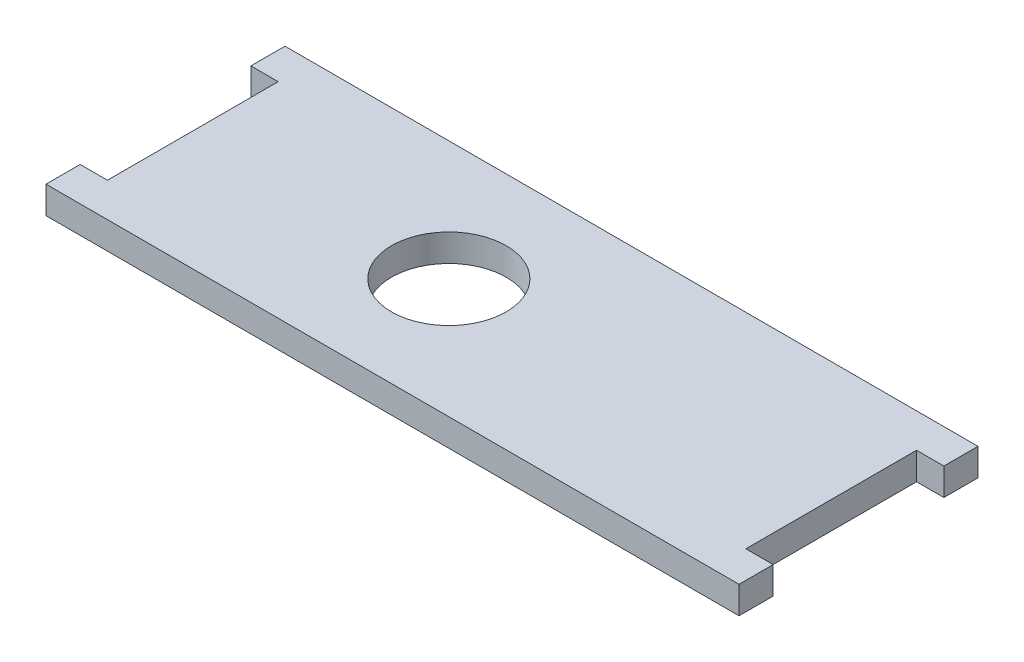
SolidWorks part; units mm, degrees
ref_plane "Front Plane" through (0, 0, 0) normal (0, 0, 1) x (1, 0, 0)
ref_plane "Top Plane" through (0, 0, 0) normal (0, 1, 0) x (1, 0, 0)
ref_plane "Right Plane" through (0, 0, 0) normal (1, 0, 0) x (0, 0, -1)
sketch "Sketch1" plane through (0, 0, 0) normal (0, 1, 0) x (1, 0, 0)
  line L1 (-59.3725, 22.225) -> (59.3725, 22.225)
  line L2 (-59.3725, 22.225) -> (-59.3725, -22.225)
  line L3 (-59.3725, -22.225) -> (59.3725, -22.225)
  line L4 (59.3725, 22.225) -> (59.3725, -22.225)
  line L5 (-59.3725, 22.225) -> (59.3725, -22.225) construction
  line L6 (-59.3725, -22.225) -> (59.3725, 22.225) construction
  line L7 (-59.3725, 22.225) -> (-64.4525, 22.225)
  line L8 (-59.3725, 22.225) -> (-59.3725, 15.875)
  line L9 (-59.3725, 15.875) -> (-64.4525, 15.875)
  line L10 (-64.4525, 22.225) -> (-64.4525, 15.875)
  line L11 (-59.3725, -22.225) -> (-64.4525, -22.225)
  line L12 (-59.3725, -22.225) -> (-59.3725, -15.875)
  line L13 (-59.3725, -15.875) -> (-64.4525, -15.875)
  line L14 (-64.4525, -22.225) -> (-64.4525, -15.875)
  line L15 (59.3725, -22.225) -> (64.4525, -22.225)
  line L16 (59.3725, -22.225) -> (59.3725, -15.875)
  line L17 (59.3725, -15.875) -> (64.4525, -15.875)
  line L18 (64.4525, -22.225) -> (64.4525, -15.875)
  line L19 (59.3725, 22.225) -> (64.4525, 22.225)
  line L20 (59.3725, 22.225) -> (59.3725, 15.875)
  line L21 (59.3725, 15.875) -> (64.4525, 15.875)
  line L22 (64.4525, 22.225) -> (64.4525, 15.875)
  circle A0 centre (-11.7475, 0) radius 10.668
  dimension "D1" = 21.336
  dimension "D2" = 118.745
  dimension "D3" = 44.45
  dimension "D4" = 5.08
  dimension "D5" = 6.35
  dimension "D6" = 47.625
extrude "Boss-Extrude1" add sketch "Sketch1" along normal blind 5.08 contours L14 L11 L2 L13 | L7 L10 L9 L2 | L4 L1 L2 L3 A0 | L22 L19 L4 L21 | L15 L18 L17 L4
